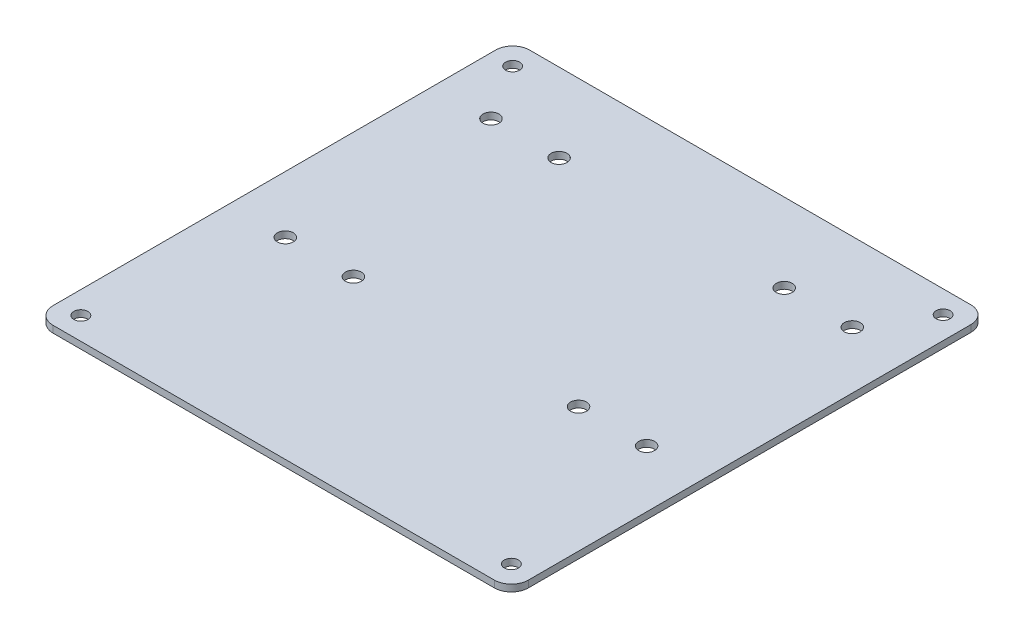
SolidWorks part; units mm, degrees
material "AISI 1020"
ref_plane "Front Plane" through (0, 0, 0) normal (0, 0, 1) x (1, 0, 0)
ref_plane "Top Plane" through (0, 0, 0) normal (0, 1, 0) x (1, 0, 0)
ref_plane "Right Plane" through (0, 0, 0) normal (1, 0, 0) x (0, 0, -1)
sketch "Sketch1" plane through (0, 0, 0) normal (0, 1, 0) x (1, 0, 0)
  line L0 (26.45, -10.82) -> (42.45, -10.82) construction
  line L1 (-55.85, 56) -> (55.85, 56)
  line L2 (-55.85, 56) -> (-55.85, -56)
  line L3 (-55.85, -56) -> (55.85, -56)
  line L4 (55.85, 56) -> (55.85, -56)
  line L5 (0, -56) -> (0, 56) construction
  line L6 (-55.85, 0) -> (55.85, 0) construction
  line L7 (-50.575, -50.725) -> (50.575, -50.725) construction
  line L8 (-50.575, -50.725) -> (-50.575, 50.725) construction
  line L9 (-50.575, 50.725) -> (50.575, 50.725) construction
  line L10 (50.575, -50.725) -> (50.575, 50.725) construction
  line L11 (-50.575, -50.725) -> (50.575, 50.725) construction
  line L12 (-50.575, 50.725) -> (50.575, -50.725) construction
  line L13 (26.45, -10.82) -> (26.45, 37.51) construction
  circle A0 centre (-50.575, 50.725) radius 1.65
  circle A1 centre (-50.575, -50.725) radius 1.65
  circle A2 centre (50.575, 50.725) radius 1.65
  circle A3 centre (50.575, -50.725) radius 1.65
  circle A4 centre (26.45, -10.82) radius 1.875
  circle A5 centre (42.45, -10.82) radius 1.875
  circle A6 centre (42.45, 37.51) radius 1.875
  circle A7 centre (26.45, 37.51) radius 1.875
  circle A8 centre (-42.45, -10.82) radius 1.875
  circle A9 centre (-26.45, -10.82) radius 1.875
  circle A10 centre (-42.45, 37.51) radius 1.875
  circle A11 centre (-26.45, 37.51) radius 1.875
  point P0 (0, 0)
  point P4 (0, 0)
  dimension "D5" = 3.3
  dimension "D6" = 3.75
  dimension "D11" = 13.4
  dimension "D1" = 112
  dimension "D2" = 111.7
  dimension "D3" = 101.15
  dimension "D4" = 101.45
  dimension "D9" = 16
  dimension "D10" = 48.33
  dimension "D12" = 45.18
  dimension "D7" = 2
  dimension "D8" = 2
extrude "Boss-Extrude1" add sketch "Sketch1" along normal blind 1.6
fillet "Fillet1" radius 4 4 edges at (-55.85, 0.8, 56) (-55.85, 0.8, -56) (55.85, 0.8, -56) (55.85, 0.8, 56)
